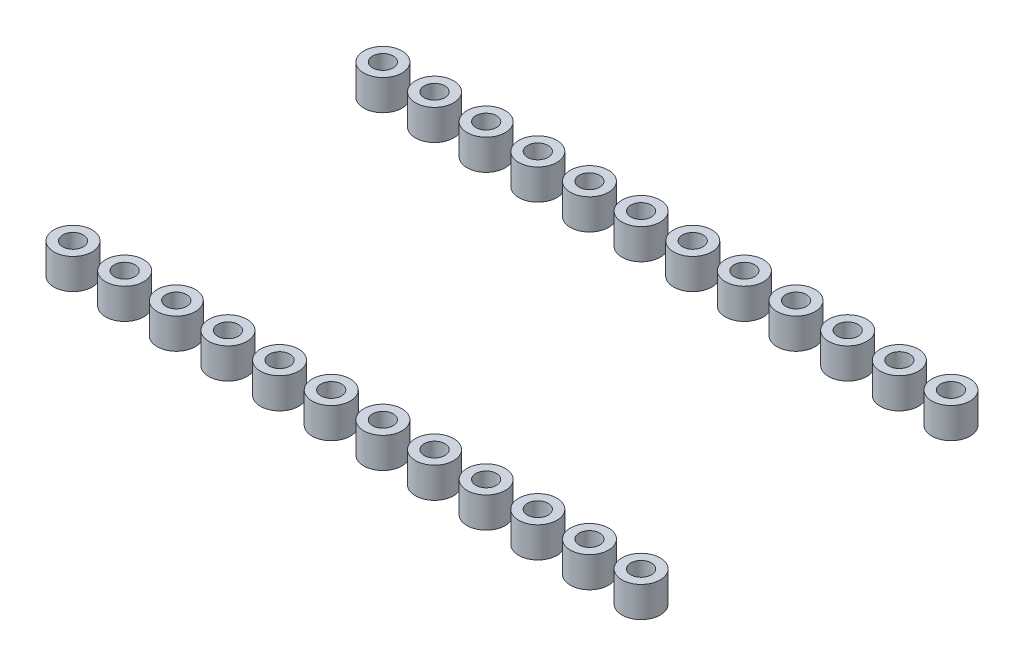
SolidWorks part; units mm, degrees
material "Pure Gold"
ref_plane "Front Plane" through (0, 0, 0) normal (0, 0, 1) x (1, 0, 0)
ref_plane "Top Plane" through (0, 0, 0) normal (0, 1, 0) x (1, 0, 0)
ref_plane "Right Plane" through (0, 0, 0) normal (1, 0, 0) x (0, 0, -1)
sketch "Sketch1" plane through (0, 0, 0) normal (0, 1, 0) x (1, 0, 0)
  circle A0 centre (-2.8151, 1.6815) radius 0.94
  circle A1 centre (-2.8151, 1.6815) radius 0.508
  circle A2 centre (-0.2751, 1.6815) radius 0.94
  circle A3 centre (-0.2751, 1.6815) radius 0.508
  circle A4 centre (2.2649, 1.6815) radius 0.94
  circle A5 centre (2.2649, 1.6815) radius 0.508
  circle A6 centre (4.8049, 1.6815) radius 0.94
  circle A7 centre (4.8049, 1.6815) radius 0.508
  circle A8 centre (7.3449, 1.6815) radius 0.94
  circle A9 centre (7.3449, 1.6815) radius 0.508
  circle A10 centre (9.8849, 1.6815) radius 0.94
  circle A11 centre (9.8849, 1.6815) radius 0.508
  circle A12 centre (12.4249, 1.6815) radius 0.94
  circle A13 centre (12.4249, 1.6815) radius 0.508
  circle A14 centre (14.9649, 1.6815) radius 0.94
  circle A15 centre (14.9649, 1.6815) radius 0.508
  circle A16 centre (17.5049, 1.6815) radius 0.94
  circle A17 centre (17.5049, 1.6815) radius 0.508
  circle A18 centre (20.0449, 1.6815) radius 0.94
  circle A19 centre (20.0449, 1.6815) radius 0.508
  circle A20 centre (22.5849, 1.6815) radius 0.94
  circle A21 centre (22.5849, 1.6815) radius 0.508
  circle A22 centre (25.1249, 1.6815) radius 0.94
  circle A23 centre (25.1249, 1.6815) radius 0.508
  circle A24 centre (-0.2751, 16.9215) radius 0.94
  circle A25 centre (-0.2751, 16.9215) radius 0.508
  circle A26 centre (2.2649, 16.9215) radius 0.94
  circle A27 centre (2.2649, 16.9215) radius 0.508
  circle A28 centre (4.8049, 16.9215) radius 0.94
  circle A29 centre (4.8049, 16.9215) radius 0.508
  circle A30 centre (7.3449, 16.9215) radius 0.94
  circle A31 centre (7.3449, 16.9215) radius 0.508
  circle A32 centre (9.8849, 16.9215) radius 0.94
  circle A33 centre (9.8849, 16.9215) radius 0.508
  circle A34 centre (12.4249, 16.9215) radius 0.94
  circle A35 centre (12.4249, 16.9215) radius 0.508
  circle A36 centre (14.9649, 16.9215) radius 0.94
  circle A37 centre (14.9649, 16.9215) radius 0.508
  circle A38 centre (17.5049, 16.9215) radius 0.94
  circle A39 centre (17.5049, 16.9215) radius 0.508
  circle A40 centre (20.0449, 16.9215) radius 0.94
  circle A41 centre (20.0449, 16.9215) radius 0.508
  circle A42 centre (22.5849, 16.9215) radius 0.94
  circle A43 centre (22.5849, 16.9215) radius 0.508
  circle A44 centre (25.1249, 16.9215) radius 0.94
  circle A45 centre (25.1249, 16.9215) radius 0.508
  circle A46 centre (-2.8151, 16.9215) radius 0.94
  circle A47 centre (-2.8151, 16.9215) radius 0.508
  dimension "D1" = 1.88
  dimension "D2" = 1.016
  dimension "D3" = 12
  dimension "D4" = 2
extrude "Boss-Extrude1" add sketch "Sketch1" along normal blind 1.5
